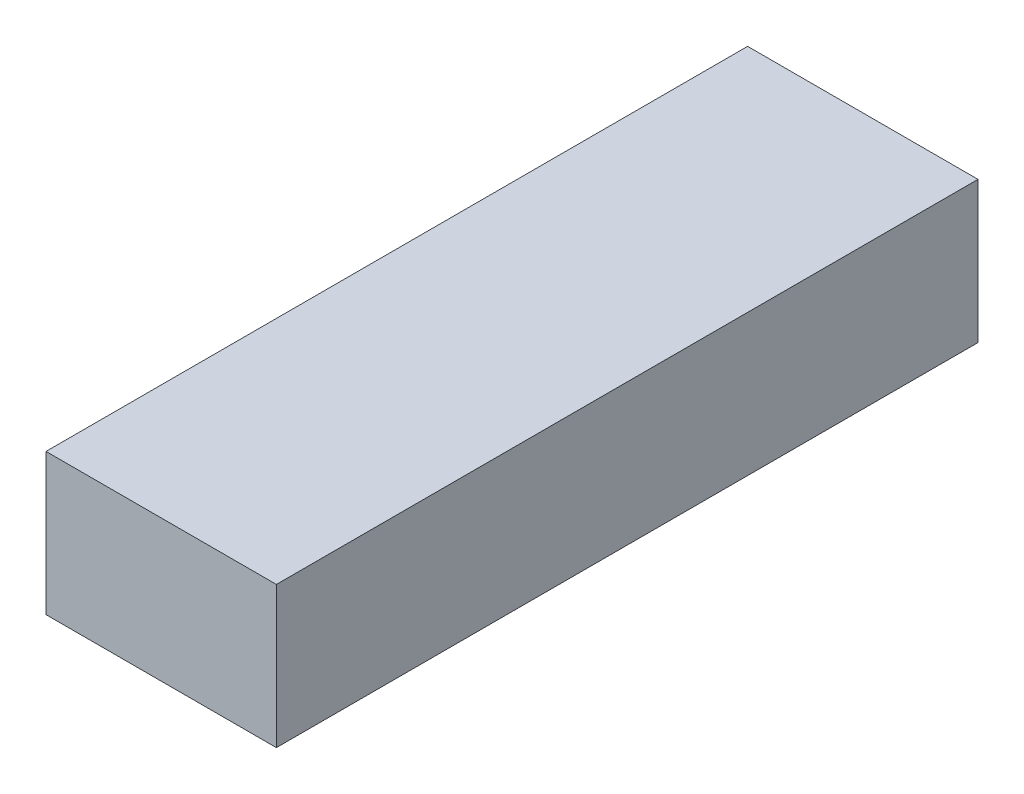
SolidWorks part; units mm, degrees
ref_plane "Front Plane" through (0, 0, 0) normal (0, 0, 1) x (1, 0, 0)
ref_plane "Top Plane" through (0, 0, 0) normal (0, 1, 0) x (1, 0, 0)
ref_plane "Right Plane" through (0, 0, 0) normal (1, 0, 0) x (0, 0, -1)
sketch "Sketch1" plane through (0, 0, 0) normal (0, 0, 1) x (1, 0, 0)
  line L1 (-22, -13.5) -> (22, -13.5)
  line L2 (-22, -13.5) -> (-22, 13.5)
  line L3 (-22, 13.5) -> (22, 13.5)
  line L4 (22, -13.5) -> (22, 13.5)
  line L5 (-22, -13.5) -> (22, 13.5) construction
  line L6 (-22, 13.5) -> (22, -13.5) construction
  point P0 (0, 0)
  dimension "D1" = 44
  dimension "D2" = 27
extrude "Boss-Extrude1" add sketch "Sketch1" along normal blind 134
